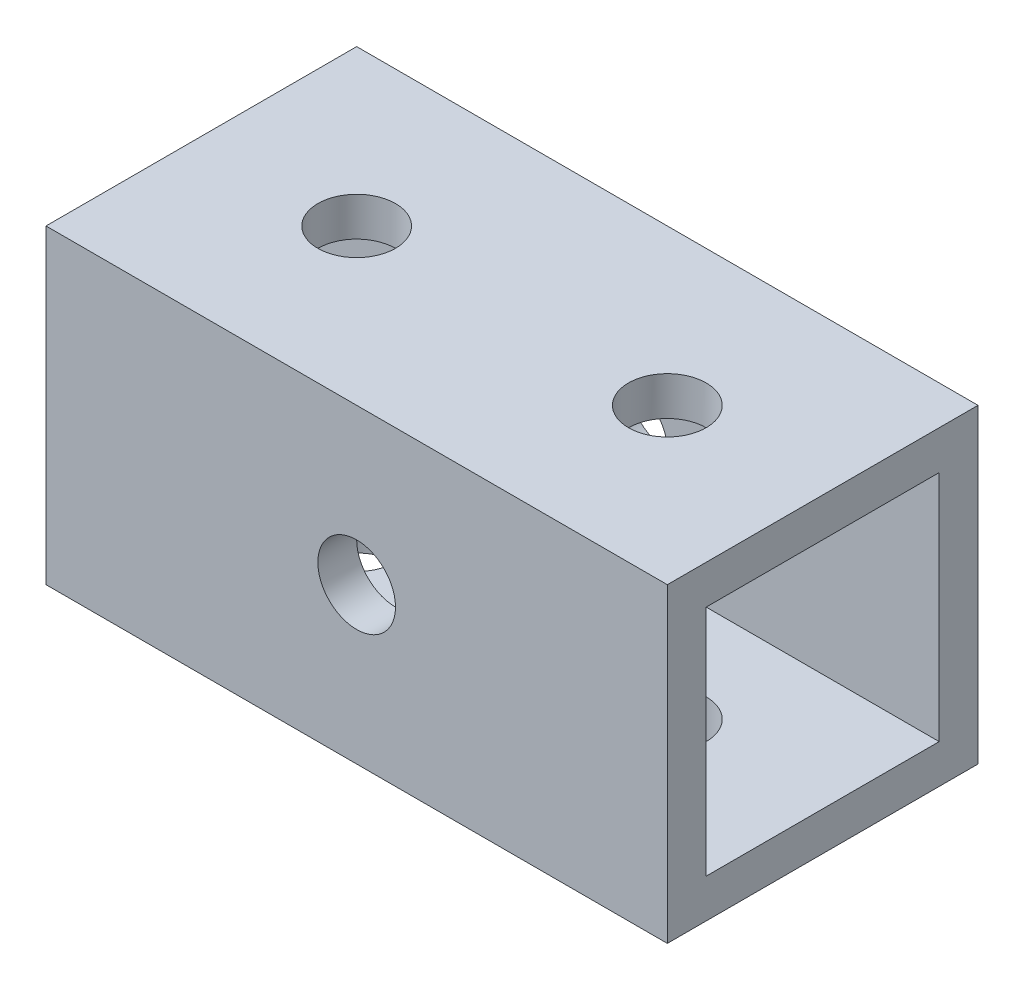
SolidWorks part; units mm, degrees
ref_plane "Front Plane" through (0, 0, 0) normal (0, 0, 1) x (1, 0, 0)
ref_plane "Top Plane" through (0, 0, 0) normal (0, 1, 0) x (1, 0, 0)
ref_plane "Right Plane" through (0, 0, 0) normal (1, 0, 0) x (0, 0, -1)
sketch "Sketch1" plane through (0, 0, 0) normal (1, 0, 0) x (0, 0, -1)
  line L0 (3.175, 3.175) -> (22.225, 3.175)
  line L1 (0, 0) -> (25.4, 0)
  line L2 (0, 0) -> (0, 25.4)
  line L3 (0, 25.4) -> (25.4, 25.4)
  line L4 (25.4, 0) -> (25.4, 25.4)
  line L5 (22.225, 3.175) -> (22.225, 22.225)
  line L6 (3.175, 22.225) -> (22.225, 22.225)
  line L7 (3.175, 3.175) -> (3.175, 22.225)
  dimension "D1" = 25.4
  dimension "D2" = 25.4
  dimension "D3" = 3.175
extrude "Extrude1" add sketch "Sketch1" along normal blind 50.8
sketch "Sketch2" plane through (0, 0, 0) normal (0, 0, 1) x (1, 0, 0)
  line L0 (25.4, 25.4) -> (25.4, 0) construction
  line L1 (50.8, 25.4) -> (0, 25.4) construction
  line L2 (50.8, 0) -> (0, 0) construction
  line L3 (0, 12.7) -> (50.8, 12.7) construction
  line L4 (0, 25.4) -> (0, 0) construction
  line L5 (50.8, 25.4) -> (50.8, 0) construction
  circle A0 centre (25.4, 12.7) radius 3.175
  dimension "D1" = 6.35
extrude "Cut-Extrude1" cut sketch "Sketch2" against normal through all
sketch "Sketch3" plane through (0, 25.4, 0) normal (0, 1, 0) x (-1, 0, 0)
  line L0 (-50.8, -12.7) -> (0, -12.7) construction
  line L1 (-50.8, -25.4) -> (-50.8, 0) construction
  line L2 (0, -25.4) -> (0, 0) construction
  line L3 (-25.4, 0) -> (-25.4, -25.4) construction
  line L4 (-50.8, 0) -> (0, 0) construction
  line L5 (-50.8, -25.4) -> (0, -25.4) construction
  circle A0 centre (-38.1, -12.7) radius 3.175
  circle A1 centre (-12.7, -12.7) radius 3.175
  dimension "D1" = 6.35
  dimension "D2" = 12.7
extrude "Cut-Extrude2" cut sketch "Sketch3" against normal through all
